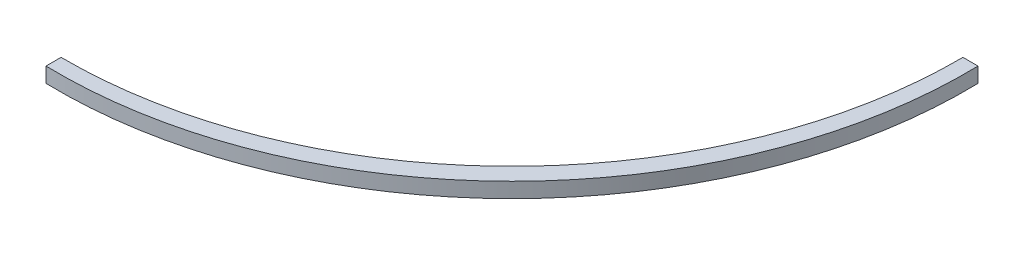
SolidWorks part; units mm, degrees
material "AISI 1020"
ref_plane "Plano frontal" through (0, 0, 0) normal (0, 0, 1) x (1, 0, 0)
ref_plane "Plano superior" through (0, 0, 0) normal (0, 1, 0) x (1, 0, 0)
ref_plane "Plano direito" through (0, 0, 0) normal (1, 0, 0) x (0, 0, -1)
sketch "Esboço1" plane through (0, 0, 0) normal (0, 1, 0) x (1, 0, 0)
  line L11 (0, -40) -> (0, 0)
  line L17 (1198.7692, 1198.7692) -> (1238.7692, 1198.7692)
  arc A0 (0, 0) -> (1198.7692, 1198.7692) centre (8.8017, 1189.9674) ccw
  arc A2 (1238.7692, 1198.7692) -> (0, -40) centre (29.1196, 1169.6496) cw
  dimension "D1" = 1190
  dimension "D3" = 40
  dimension "D4" = 40
extrude "Ressalto-extrusão1" add sketch "Esboço1" along normal blind 40 contours A0 L17 A2 L11
